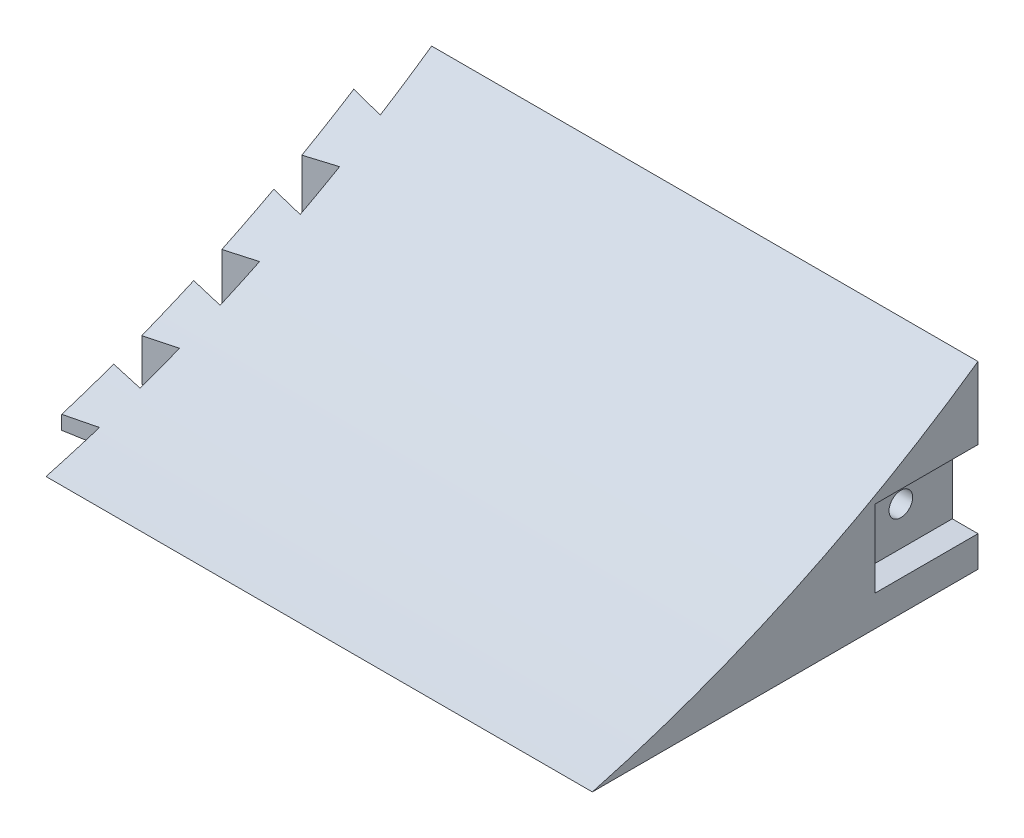
SolidWorks part; units mm, degrees
ref_plane "Front Plane" through (0, 0, 0) normal (0, 0, 1) x (1, 0, 0)
ref_plane "Top Plane" through (0, 0, 0) normal (0, 1, 0) x (1, 0, 0)
ref_plane "Right Plane" through (0, 0, 0) normal (1, 0, 0) x (0, 0, -1)
sketch "Sketch3" plane through (0, 0, 0) normal (1, 0, 0) x (0, 0, -1)
  line L0 (0, 0) -> (95.25, 0)
  line L1 (95.25, 0) -> (95.25, 44.45)
  arc A0 (0, 0) -> (95.25, 44.45) centre (-79.3399, 294.2927) ccw
  dimension "D3" = 304.8
  dimension "D1" = 44.45
  dimension "D2" = 95.25
extrude "Boss-Extrude1" add sketch "Sketch3" along normal blind 134.9375
sketch "Sketch4" plane through (134.9375, 0, 0) normal (1, 0, 0) x (0, 0, -1)
  line L0 (95.25, 0) -> (95.25, 44.45) construction
  line L1 (95.25, 26.67) -> (69.85, 26.67)
  line L2 (95.25, 26.67) -> (95.25, 7.62)
  line L3 (95.25, 7.62) -> (69.85, 7.62)
  line L4 (69.85, 26.67) -> (69.85, 7.62)
  line L5 (0, 0) -> (95.25, 0) construction
  dimension "D1" = 19.05
  dimension "D2" = 7.62
  dimension "D3" = 25.4
extrude "Cut-Extrude1" cut sketch "Sketch4" against normal blind 6.35
sketch "Sketch6" plane through (128.5875, 0, 0) normal (1, 0, 0) x (0, 0, -1)
  line L0 (95.25, 7.62) -> (95.25, 26.67) construction
  line L1 (95.25, 26.67) -> (69.85, 26.67) construction
  circle A0 centre (82.55, 17.145) radius 2.921
  dimension "D1" = 5.842
  dimension "D2" = 12.7
  dimension "D3" = 9.525
extrude "Cut-Extrude3" cut sketch "Sketch6" against normal blind 25.4
sketch "Sketch7" plane through (0, 0, 0) normal (0, -1, 0) x (1, 0, 0)
  line L0 (0, -82.55) -> (-7.9228, -83.947)
  line L1 (0, 0) -> (0, -95.25) construction
  line L2 (-7.9228, -83.947) -> (-7.9228, -71.12)
  line L3 (-7.9228, -71.12) -> (0, -72.517)
  line L4 (0, -82.55) -> (0, -72.517)
  line L5 (0, -62.7803) -> (-7.9228, -64.1773)
  line L6 (0, -62.7803) -> (0, -52.7473)
  line L7 (-7.9228, -51.3503) -> (0, -52.7473)
  line L8 (-7.9228, -64.1773) -> (-7.9228, -51.3503)
  line L9 (0, -43.0107) -> (-7.9228, -44.4077)
  line L10 (0, -43.0107) -> (0, -32.9777)
  line L11 (-7.9228, -31.5807) -> (0, -32.9777)
  line L12 (-7.9228, -44.4077) -> (-7.9228, -31.5807)
  line L13 (0, -23.241) -> (-7.9228, -24.638)
  line L14 (0, -23.241) -> (0, -13.208)
  line L15 (-7.9228, -11.811) -> (0, -13.208)
  line L16 (-7.9228, -24.638) -> (-7.9228, -11.811)
  dimension "D1" = 12.827
  dimension "D2" = 80
  dimension "D3" = 80
  dimension "D4" = 4
  dimension "D5" = 10.033
  dimension "D6" = 12.7
  dimension "D7" = 13.208
extrude "Boss-Extrude2" add sketch "Sketch7" against normal blind 38.1
sketch "Sketch8" plane through (134.9375, 0, 0) normal (1, 0, 0) x (0, 0, -1)
  line L1 (95.25, 44.45) -> (0, 44.45)
  line L2 (0, 44.45) -> (0, 0)
  arc A0 (0, 0) -> (95.25, 44.45) centre (-79.3399, 294.2927) ccw
  arc A1 (0, 0) -> (95.25, 44.45) centre (-79.3399, 294.2927) ccw construction
extrude "Cut-Extrude4" cut sketch "Sketch8" against normal through all
